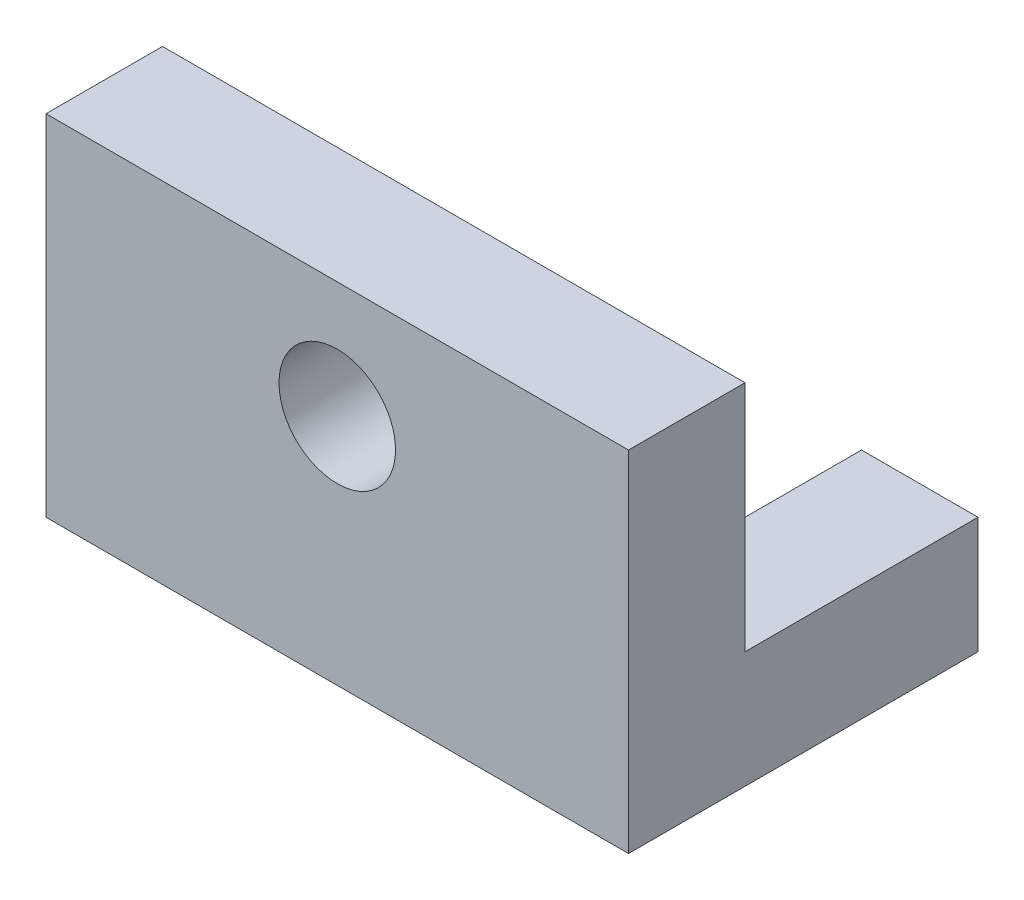
SolidWorks part; units mm, degrees
ref_plane "Front Plane" through (0, 0, 0) normal (0, 0, 1) x (1, 0, 0)
ref_plane "Top Plane" through (0, 0, 0) normal (0, 1, 0) x (1, 0, 0)
ref_plane "Right Plane" through (0, 0, 0) normal (1, 0, 0) x (0, 0, -1)
sketch "Sketch1" plane through (0, 0, 0) normal (1, 0, 0) x (0, 0, -1)
  line L0 (0, 0) -> (60, 0)
  line L1 (0, 0) -> (0, 60)
  line L2 (20, 20) -> (20, 60)
  line L3 (20, 20) -> (60, 20)
  line L4 (0, 60) -> (20, 60)
  line L5 (60, 0) -> (60, 20)
  dimension "D1" = 60
  dimension "D2" = 60
  dimension "D3" = 20
extrude "Boss-Extrude1" add sketch "Sketch1" along normal mid plane 100
sketch "Sketch2" plane through (0, 0, -20) normal (0, 0, -1) x (-1, 0, 0)
  line L0 (-50, 60) -> (50, 60) construction
  line L1 (0, 60) -> (0, 40) construction
  circle A0 centre (0, 40) radius 10
  dimension "D1" = 20
  dimension "D2" = 20
extrude "Cut-Extrude1" cut sketch "Sketch2" against normal through all
sketch "Sketch3" plane through (0, 20, 0) normal (0, 1, 0) x (1, 0, 0)
  line L0 (50, 60) -> (-50, 60) construction
  line L1 (-30, 60) -> (30, 60)
  line L2 (-30, 60) -> (-30, 40)
  line L3 (-30, 40) -> (30, 40)
  line L4 (30, 60) -> (30, 40)
  line L5 (50, 60) -> (50, 20) construction
  dimension "D1" = 60
  dimension "D2" = 20
  dimension "D3" = 20
extrude "Cut-Extrude2" cut sketch "Sketch3" against normal up to next
